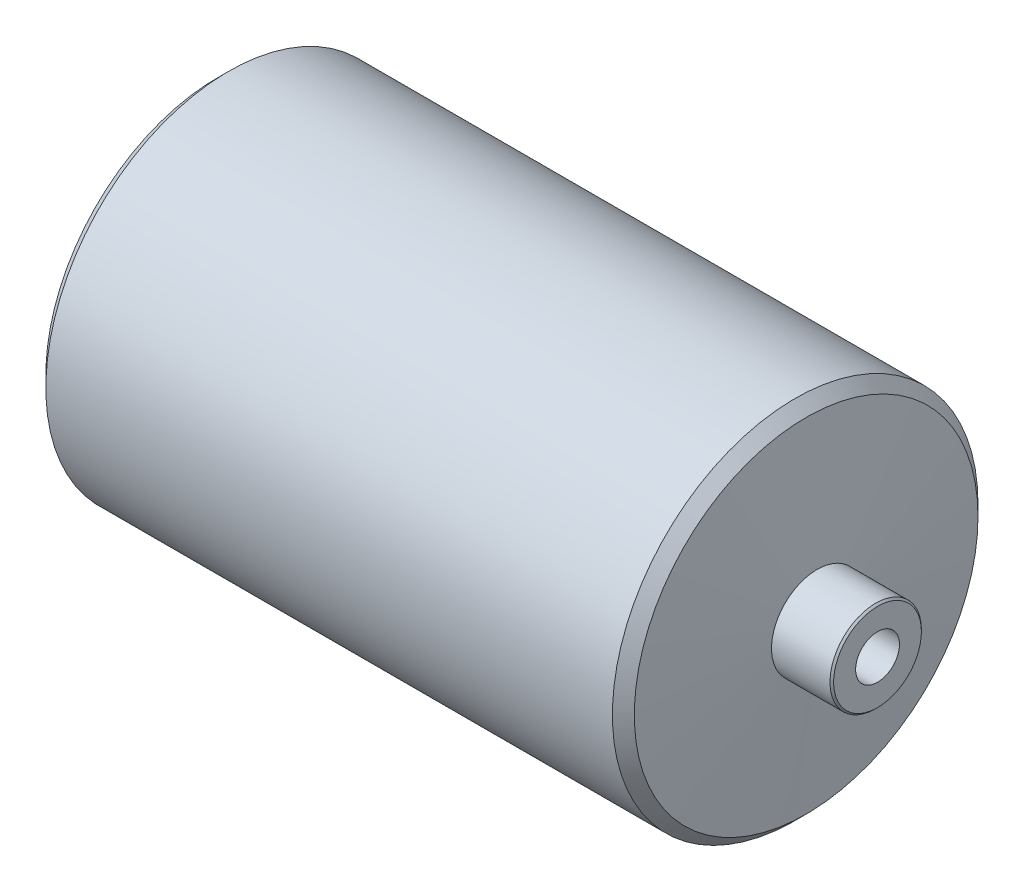
SolidWorks part; units mm, degrees
ref_plane "Alzado" through (0, 0, 0) normal (0, 0, 1) x (1, 0, 0)
ref_plane "Planta" through (0, 0, 0) normal (0, 1, 0) x (1, 0, 0)
ref_plane "Vista lateral" through (0, 0, 0) normal (1, 0, 0) x (0, 0, -1)
sketch "Croquis1" plane through (0, 0, 0) normal (0, 0, 1) x (1, 0, 0)
  line L0 (112.2449, 0) -> (-112.2449, 0) construction
  line L1 (0, 0) -> (0, 58.9054) construction
  line L2 (100, 0) -> (100, 12)
  line L3 (99.5, 12.5) -> (83.5, 12.5)
  line L4 (83.5, 12.5) -> (80.4816, 47)
  line L5 (80.4816, 47) -> (77.4816, 50)
  line L6 (77.4816, 50) -> (-77.4816, 50)
  line L7 (-100, 0) -> (100, 0)
  line L8 (100, 12) -> (99.5, 12.5)
  line L9 (-100, 0) -> (-100, 12)
  line L10 (-100, 12) -> (-99.5, 12.5)
  line L11 (-99.5, 12.5) -> (-83.5, 12.5)
  line L12 (-83.5, 12.5) -> (-80.4816, 47)
  line L13 (-80.4816, 47) -> (-77.4816, 50)
  point P4 (0, 0)
  point P8 (100, 12.5)
  point P9 (80.5597, 46.1074)
  point P21 (0, 50)
  dimension "D1" = 100
  dimension "D2" = 25
  dimension "D3" = 16.5
  dimension "D4" = 85
  dimension "D5" = 100
  dimension "D6" = 3
  dimension "D7" = 3
revolve "Revolución1" add sketch "Croquis1" angle 360 about L0
sketch "Croquis7" plane through (-100, 0, 0) normal (-1, 0, 0) x (0, 0, 1)
  point P0 (0, 0)
hole_wizard "Taladro de margen para M101" positions "Croquis3D5" profile "Croquis8" hole size "M10" standard "GB"
sketch3d "Croquis3D5"
  point P0 (0, 0, 0)
  point P3 (-100, 0, 0)
sketch "Croquis8" plane through (-100, 0, 0) normal (0, 1, 0) x (0, 0, 1)
  line L0 (0, 0) -> (0, 59)
  line L1 (0, 59) -> (6, 55.3948)
  line L2 (6, 55.3948) -> (6, 0)
  line L5 (6, 0) -> (0, 0)
  line L10 (0, 59) -> (-6, 55.3948) construction
  line L11 (0, -6.35) -> (0, 107.95) construction
  dimension "Diámetro de taladro" = 12
  dimension "Profundidad de taladro" = 59
  dimension "Ángulo de perforador" = 118
sketch "Croquis9" plane through (100, 0, 0) normal (1, 0, 0) x (0, 0, -1)
  point P0 (0, 0)
hole_wizard "Taladro de margen para M102" positions "Croquis3D6" profile "Croquis10" hole size "M10" standard "GB"
sketch3d "Croquis3D6"
  point P0 (100, 0, 0)
sketch "Croquis10" plane through (100, 0, 0) normal (0, 1, 0) x (0, 0, -1)
  line L0 (0, 0) -> (0, 59)
  line L1 (0, 59) -> (6, 55.3948)
  line L2 (6, 55.3948) -> (6, 0)
  line L5 (6, 0) -> (0, 0)
  line L10 (0, 59) -> (-6, 55.3948) construction
  line L11 (0, -6.35) -> (0, 107.95) construction
  dimension "Diámetro de taladro" = 12
  dimension "Profundidad de taladro" = 59
  dimension "Ángulo de perforador" = 118
